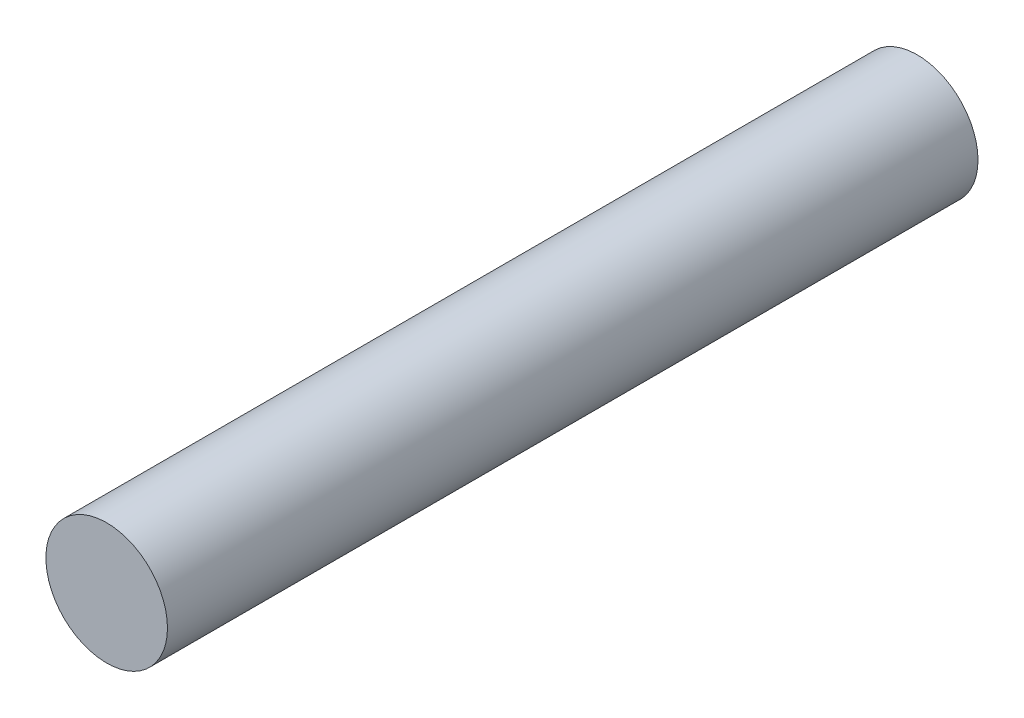
SolidWorks part; units mm, degrees
ref_plane "Front Plane" through (0, 0, 0) normal (0, 0, 1) x (1, 0, 0)
ref_plane "Top Plane" through (0, 0, 0) normal (0, 1, 0) x (1, 0, 0)
ref_plane "Right Plane" through (0, 0, 0) normal (1, 0, 0) x (0, 0, -1)
sketch "Sketch1" plane through (0, 0, 0) normal (0, 0, 1) x (1, 0, 0)
  circle A0 centre (-13.468, 10.061) radius 3
  dimension "D1" = 6
extrude "Boss-Extrude1" add sketch "Sketch1" along normal blind 40
